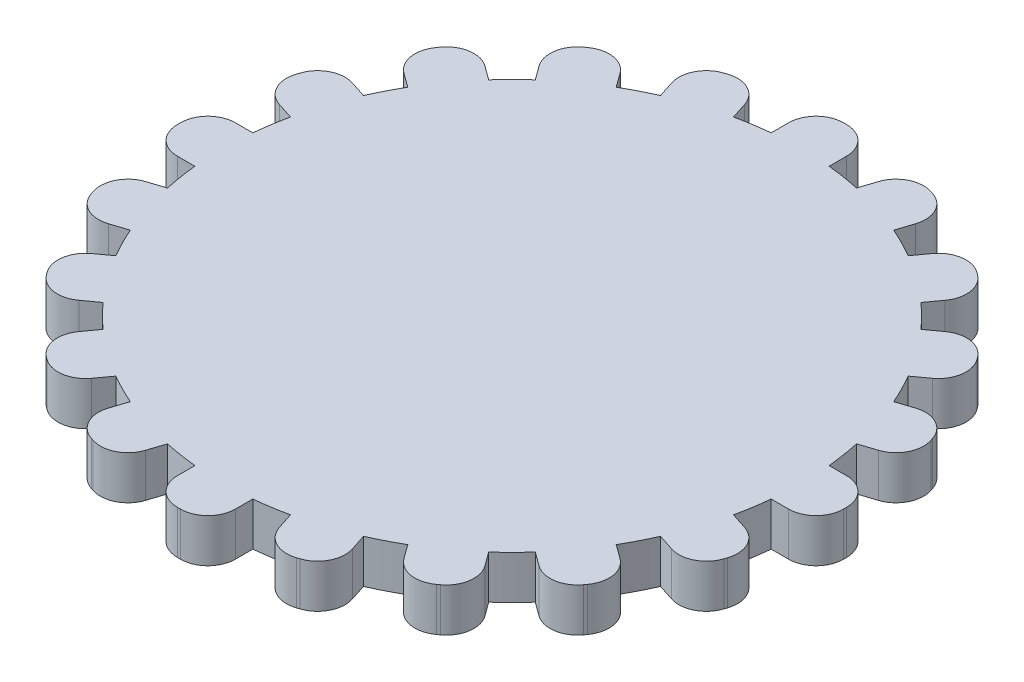
SolidWorks part; units mm, degrees
ref_plane "Front Plane" through (0, 0, 0) normal (0, 0, 1) x (1, 0, 0)
ref_plane "Top Plane" through (0, 0, 0) normal (0, 1, 0) x (1, 0, 0)
ref_plane "Right Plane" through (0, 0, 0) normal (1, 0, 0) x (0, 0, -1)
sketch "Sketch1" plane through (0, 0, 0) normal (0, 1, 0) x (1, 0, 0)
  line L0 (0, -10) -> (0, -1.5)
  line L50 (0, 1.5) -> (0, 10)
  line L51 (-2.5, -1.5) -> (2.5, -1.5)
  line L52 (-13, 0) -> (13, 0)
  line L53 (-13, -0.1) -> (-13, 0.1)
  line L54 (-11.1, 2) -> (-9.798, 2)
  line L55 (-11.1, -2) -> (-9.798, -2)
  line L56 (-2.5, -1.5) -> (-2.5, 1.5)
  line L57 (-7.8045, 8.1425) -> (-6.7511, 7.3771)
  line L58 (-10.576, 7.5603) -> (-10.4584, 7.7221)
  line L59 (-10.1557, 4.9064) -> (-9.1023, 4.1411)
  line L60 (-1.528, 11.1748) -> (-1.1256, 9.9364)
  line L61 (-4.1123, 12.3328) -> (-3.9221, 12.3946)
  line L62 (-5.3322, 9.9387) -> (-4.9298, 8.7004)
  line L63 (5.3322, 9.9387) -> (4.9298, 8.7004)
  line L64 (3.9221, 12.3946) -> (4.1123, 12.3328)
  line L65 (1.528, 11.1748) -> (1.1256, 9.9364)
  line L66 (10.1557, 4.9064) -> (9.1023, 4.1411)
  line L67 (10.4584, 7.7221) -> (10.576, 7.5603)
  line L68 (7.8045, 8.1425) -> (6.7511, 7.3771)
  line L69 (11.1, -2) -> (9.798, -2)
  line L70 (13, 0.1) -> (13, -0.1)
  line L71 (11.1, 2) -> (9.798, 2)
  line L72 (7.8045, -8.1425) -> (6.7511, -7.3771)
  line L73 (10.576, -7.5603) -> (10.4584, -7.7221)
  line L74 (10.1557, -4.9064) -> (9.1023, -4.1411)
  line L75 (1.528, -11.1748) -> (1.1256, -9.9364)
  line L76 (4.1123, -12.3328) -> (3.9221, -12.3946)
  line L77 (5.3322, -9.9387) -> (4.9298, -8.7004)
  line L78 (-5.3322, -9.9387) -> (-4.9298, -8.7004)
  line L79 (-3.9221, -12.3946) -> (-4.1123, -12.3328)
  line L80 (-1.528, -11.1748) -> (-1.1256, -9.9364)
  line L81 (-10.1557, -4.9064) -> (-9.1023, -4.1411)
  line L82 (-10.4584, -7.7221) -> (-10.576, -7.5603)
  line L83 (-7.8045, -8.1425) -> (-6.7511, -7.3771)
  line L84 (-2.5, 1.5) -> (2.5, 1.5)
  line L85 (2.5, -1.5) -> (2.5, 1.5)
  line L86 (-2.5, -1.5) -> (2.5, 1.5) construction
  line L87 (-2.5, 1.5) -> (2.5, -1.5) construction
  arc A13 (-9.1023, 4.1411) -> (-9.798, 2) centre (0, 0) ccw
  arc A14 (-13, 0.1) -> (-11.1, 2) centre (-11.1, 0.1) cw
  arc A15 (-13, -0.1) -> (-11.1, -2) centre (-11.1, -0.1) ccw
  arc A16 (-10.4584, 7.7221) -> (-7.8045, 8.1425) centre (-8.9213, 6.6053) cw
  arc A17 (-10.576, 7.5603) -> (-10.1557, 4.9064) centre (-9.0389, 6.4435) ccw
  arc A18 (-3.9221, 12.3946) -> (-1.528, 11.1748) centre (-3.335, 10.5876) cw
  arc A19 (-4.1123, 12.3328) -> (-5.3322, 9.9387) centre (-3.5252, 10.5258) ccw
  arc A20 (4.1123, 12.3328) -> (5.3322, 9.9387) centre (3.5252, 10.5258) cw
  arc A21 (3.9221, 12.3946) -> (1.528, 11.1748) centre (3.335, 10.5876) ccw
  arc A22 (10.576, 7.5603) -> (10.1557, 4.9064) centre (9.0389, 6.4435) cw
  arc A23 (10.4584, 7.7221) -> (7.8045, 8.1425) centre (8.9213, 6.6053) ccw
  arc A24 (13, -0.1) -> (11.1, -2) centre (11.1, -0.1) cw
  arc A25 (13, 0.1) -> (11.1, 2) centre (11.1, 0.1) ccw
  arc A26 (10.4584, -7.7221) -> (7.8045, -8.1425) centre (8.9213, -6.6053) cw
  arc A27 (10.576, -7.5603) -> (10.1557, -4.9064) centre (9.0389, -6.4435) ccw
  arc A28 (3.9221, -12.3946) -> (1.528, -11.1748) centre (3.335, -10.5876) cw
  arc A29 (4.1123, -12.3328) -> (5.3322, -9.9387) centre (3.5252, -10.5258) ccw
  arc A30 (-4.1123, -12.3328) -> (-5.3322, -9.9387) centre (-3.5252, -10.5258) cw
  arc A31 (-3.9221, -12.3946) -> (-1.528, -11.1748) centre (-3.335, -10.5876) ccw
  arc A32 (-10.576, -7.5603) -> (-10.1557, -4.9064) centre (-9.0389, -6.4435) cw
  arc A33 (-10.4584, -7.7221) -> (-7.8045, -8.1425) centre (-8.9213, -6.6053) ccw
  arc A34 (-4.9298, 8.7004) -> (-6.7511, 7.3771) centre (0, 0) ccw
  arc A35 (1.1256, 9.9364) -> (-1.1256, 9.9364) centre (0, 0) ccw
  arc A36 (6.7511, 7.3771) -> (4.9298, 8.7004) centre (0, 0) ccw
  arc A37 (9.798, 2) -> (9.1023, 4.1411) centre (0, 0) ccw
  arc A38 (9.1023, -4.1411) -> (9.798, -2) centre (0, 0) ccw
  arc A39 (4.9298, -8.7004) -> (6.7511, -7.3771) centre (0, 0) ccw
  arc A40 (-1.1256, -9.9364) -> (1.1256, -9.9364) centre (0, 0) ccw
  arc A41 (-6.7511, -7.3771) -> (-4.9298, -8.7004) centre (0, 0) ccw
  arc A42 (-9.798, -2) -> (-9.1023, -4.1411) centre (0, 0) ccw
  point P6 (0, 0)
  point P8 (0, 0)
  point P9 (0, 0)
  point P17 (0, 0)
  point P18 (0, 0)
  point P22 (-13, 2)
  point P63 (0, 0)
  point P119 (0, 0)
  dimension "D1" = 20
  dimension "D2" = 26
  dimension "D4" = 1.9
  dimension "D3" = 2
  dimension "D5" = 10
  dimension "D6" = 3
  dimension "D7" = 5
sketch "Sketch2" plane through (0, 0, 0) normal (0, 1, 0) x (1, 0, 0)
  line L0 (-2, 0) -> (2, 0)
  line L1 (-23, -0.1) -> (-23, 0.1)
  line L2 (-21.1, 2) -> (-19.8997, 2)
  line L3 (-21.1, -2) -> (-19.8997, -2)
  line L4 (-20.6853, 4.6181) -> (-19.5438, 4.2472)
  line L5 (-19.4493, 8.4224) -> (-18.3078, 8.0515)
  line L6 (-21.9052, 7.0123) -> (-21.8434, 7.2025)
  line L7 (-18.2458, 10.7842) -> (-17.2748, 10.0787)
  line L8 (-15.8947, 14.0203) -> (-14.9237, 13.3148)
  line L9 (-18.6662, 13.4382) -> (-18.5486, 13.6)
  line L10 (-14.0203, 15.8947) -> (-13.3148, 14.9237)
  line L11 (-10.7842, 18.2458) -> (-10.0787, 17.2748)
  line L12 (-13.6, 18.5486) -> (-13.4382, 18.6662)
  line L13 (-8.4224, 19.4493) -> (-8.0515, 18.3078)
  line L14 (-4.6181, 20.6853) -> (-4.2472, 19.5438)
  line L15 (-7.2025, 21.8434) -> (-7.0123, 21.9052)
  line L16 (-2, 21.1) -> (-2, 19.8997)
  line L17 (2, 21.1) -> (2, 19.8997)
  line L18 (-0.1, 23) -> (0.1, 23)
  line L19 (4.6181, 20.6853) -> (4.2472, 19.5438)
  line L20 (8.4224, 19.4493) -> (8.0515, 18.3078)
  line L21 (7.0123, 21.9052) -> (7.2025, 21.8434)
  line L22 (10.7842, 18.2458) -> (10.0787, 17.2748)
  line L23 (14.0203, 15.8947) -> (13.3148, 14.9237)
  line L24 (13.4382, 18.6662) -> (13.6, 18.5486)
  line L25 (15.8947, 14.0203) -> (14.9237, 13.3148)
  line L26 (18.2458, 10.7842) -> (17.2748, 10.0787)
  line L27 (18.5486, 13.6) -> (18.6662, 13.4382)
  line L28 (19.4493, 8.4224) -> (18.3078, 8.0515)
  line L29 (20.6853, 4.6181) -> (19.5438, 4.2472)
  line L30 (21.8434, 7.2025) -> (21.9052, 7.0123)
  line L31 (21.1, 2) -> (19.8997, 2)
  line L32 (21.1, -2) -> (19.8997, -2)
  line L33 (23, 0.1) -> (23, -0.1)
  line L34 (20.6853, -4.6181) -> (19.5438, -4.2472)
  line L35 (19.4493, -8.4224) -> (18.3078, -8.0515)
  line L36 (21.9052, -7.0123) -> (21.8434, -7.2025)
  line L37 (18.2458, -10.7842) -> (17.2748, -10.0787)
  line L38 (15.8947, -14.0203) -> (14.9237, -13.3148)
  line L39 (18.6662, -13.4382) -> (18.5486, -13.6)
  line L40 (14.0203, -15.8947) -> (13.3148, -14.9237)
  line L41 (10.7842, -18.2458) -> (10.0787, -17.2748)
  line L42 (13.6, -18.5486) -> (13.4382, -18.6662)
  line L43 (8.4224, -19.4493) -> (8.0515, -18.3078)
  line L44 (4.6181, -20.6853) -> (4.2472, -19.5438)
  line L45 (7.2025, -21.8434) -> (7.0123, -21.9052)
  line L46 (2, -21.1) -> (2, -19.8997)
  line L47 (-2, -21.1) -> (-2, -19.8997)
  line L48 (0.1, -23) -> (-0.1, -23)
  line L49 (-4.6181, -20.6853) -> (-4.2472, -19.5438)
  line L50 (-8.4224, -19.4493) -> (-8.0515, -18.3078)
  line L51 (-7.0123, -21.9052) -> (-7.2025, -21.8434)
  line L52 (-10.7842, -18.2458) -> (-10.0787, -17.2748)
  line L53 (-14.0203, -15.8947) -> (-13.3148, -14.9237)
  line L54 (-13.4382, -18.6662) -> (-13.6, -18.5486)
  line L55 (-15.8947, -14.0203) -> (-14.9237, -13.3148)
  line L56 (-18.2458, -10.7842) -> (-17.2748, -10.0787)
  line L57 (-18.5486, -13.6) -> (-18.6662, -13.4382)
  line L58 (-19.4493, -8.4224) -> (-18.3078, -8.0515)
  line L59 (-20.6853, -4.6181) -> (-19.5438, -4.2472)
  line L60 (-21.8434, -7.2025) -> (-21.9052, -7.0123)
  arc A0 (-18.3078, -8.0515) -> (-17.2748, -10.0787) centre (0, 0) ccw
  arc A1 (-21.1, 2) -> (-23, 0.1) centre (-21.1, 0.1) ccw
  arc A2 (-21.1, -2) -> (-23, -0.1) centre (-21.1, -0.1) cw
  arc A3 (-20.6853, 4.6181) -> (-21.9052, 7.0123) centre (-20.0982, 6.4252) cw
  arc A4 (-19.4493, 8.4224) -> (-21.8434, 7.2025) centre (-20.0364, 6.6154) ccw
  arc A5 (-18.2458, 10.7842) -> (-18.6662, 13.4382) centre (-17.129, 12.3214) cw
  arc A6 (-15.8947, 14.0203) -> (-18.5486, 13.6) centre (-17.0115, 12.4832) ccw
  arc A7 (-14.0203, 15.8947) -> (-13.6, 18.5486) centre (-12.4832, 17.0115) cw
  arc A8 (-10.7842, 18.2458) -> (-13.4382, 18.6662) centre (-12.3214, 17.129) ccw
  arc A9 (-8.4224, 19.4493) -> (-7.2025, 21.8434) centre (-6.6154, 20.0364) cw
  arc A10 (-4.6181, 20.6853) -> (-7.0123, 21.9052) centre (-6.4252, 20.0982) ccw
  arc A11 (-2, 21.1) -> (-0.1, 23) centre (-0.1, 21.1) cw
  arc A12 (2, 21.1) -> (0.1, 23) centre (0.1, 21.1) ccw
  arc A13 (4.6181, 20.6853) -> (7.0123, 21.9052) centre (6.4252, 20.0982) cw
  arc A14 (8.4224, 19.4493) -> (7.2025, 21.8434) centre (6.6154, 20.0364) ccw
  arc A15 (10.7842, 18.2458) -> (13.4382, 18.6662) centre (12.3214, 17.129) cw
  arc A16 (14.0203, 15.8947) -> (13.6, 18.5486) centre (12.4832, 17.0115) ccw
  arc A17 (15.8947, 14.0203) -> (18.5486, 13.6) centre (17.0115, 12.4832) cw
  arc A18 (18.2458, 10.7842) -> (18.6662, 13.4382) centre (17.129, 12.3214) ccw
  arc A19 (19.4493, 8.4224) -> (21.8434, 7.2025) centre (20.0364, 6.6154) cw
  arc A20 (20.6853, 4.6181) -> (21.9052, 7.0123) centre (20.0982, 6.4252) ccw
  arc A21 (21.1, 2) -> (23, 0.1) centre (21.1, 0.1) cw
  arc A22 (21.1, -2) -> (23, -0.1) centre (21.1, -0.1) ccw
  arc A23 (20.6853, -4.6181) -> (21.9052, -7.0123) centre (20.0982, -6.4252) cw
  arc A24 (19.4493, -8.4224) -> (21.8434, -7.2025) centre (20.0364, -6.6154) ccw
  arc A25 (18.2458, -10.7842) -> (18.6662, -13.4382) centre (17.129, -12.3214) cw
  arc A26 (15.8947, -14.0203) -> (18.5486, -13.6) centre (17.0115, -12.4832) ccw
  arc A27 (14.0203, -15.8947) -> (13.6, -18.5486) centre (12.4832, -17.0115) cw
  arc A28 (10.7842, -18.2458) -> (13.4382, -18.6662) centre (12.3214, -17.129) ccw
  arc A29 (8.4224, -19.4493) -> (7.2025, -21.8434) centre (6.6154, -20.0364) cw
  arc A30 (4.6181, -20.6853) -> (7.0123, -21.9052) centre (6.4252, -20.0982) ccw
  arc A31 (2, -21.1) -> (0.1, -23) centre (0.1, -21.1) cw
  arc A32 (-2, -21.1) -> (-0.1, -23) centre (-0.1, -21.1) ccw
  arc A33 (-4.6181, -20.6853) -> (-7.0123, -21.9052) centre (-6.4252, -20.0982) cw
  arc A34 (-8.4224, -19.4493) -> (-7.2025, -21.8434) centre (-6.6154, -20.0364) ccw
  arc A35 (-10.7842, -18.2458) -> (-13.4382, -18.6662) centre (-12.3214, -17.129) cw
  arc A36 (-14.0203, -15.8947) -> (-13.6, -18.5486) centre (-12.4832, -17.0115) ccw
  arc A37 (-15.8947, -14.0203) -> (-18.5486, -13.6) centre (-17.0115, -12.4832) cw
  arc A38 (-18.2458, -10.7842) -> (-18.6662, -13.4382) centre (-17.129, -12.3214) ccw
  arc A39 (-19.4493, -8.4224) -> (-21.8434, -7.2025) centre (-20.0364, -6.6154) cw
  arc A40 (-20.6853, -4.6181) -> (-21.9052, -7.0123) centre (-20.0982, -6.4252) ccw
  arc A41 (-19.8997, -2) -> (-19.5438, -4.2472) centre (0, 0) ccw
  arc A42 (-19.5438, 4.2472) -> (-19.8997, 2) centre (0, 0) ccw
  arc A43 (-17.2748, 10.0787) -> (-18.3078, 8.0515) centre (0, 0) ccw
  arc A44 (-13.3148, 14.9237) -> (-14.9237, 13.3148) centre (0, 0) ccw
  arc A45 (-8.0515, 18.3078) -> (-10.0787, 17.2748) centre (0, 0) ccw
  arc A46 (-2, 19.8997) -> (-4.2472, 19.5438) centre (0, 0) ccw
  arc A47 (4.2472, 19.5438) -> (2, 19.8997) centre (0, 0) ccw
  arc A48 (10.0787, 17.2748) -> (8.0515, 18.3078) centre (0, 0) ccw
  arc A49 (14.9237, 13.3148) -> (13.3148, 14.9237) centre (0, 0) ccw
  arc A50 (18.3078, 8.0515) -> (17.2748, 10.0787) centre (0, 0) ccw
  arc A51 (19.8997, 2) -> (19.5438, 4.2472) centre (0, 0) ccw
  arc A52 (19.5438, -4.2472) -> (19.8997, -2) centre (0, 0) ccw
  arc A53 (17.2748, -10.0787) -> (18.3078, -8.0515) centre (0, 0) ccw
  arc A54 (13.3148, -14.9237) -> (14.9237, -13.3148) centre (0, 0) ccw
  arc A55 (8.0515, -18.3078) -> (10.0787, -17.2748) centre (0, 0) ccw
  arc A56 (2, -19.8997) -> (4.2472, -19.5438) centre (0, 0) ccw
  arc A57 (-10.0787, -17.2748) -> (-8.0515, -18.3078) centre (0, 0) ccw
  arc A58 (-4.2472, -19.5438) -> (-2, -19.8997) centre (0, 0) ccw
  arc A59 (-14.9237, -13.3148) -> (-13.3148, -14.9237) centre (0, 0) ccw
  point P6 (0, 0)
  point P10 (-23, 2)
  point P170 (0, 0)
  dimension "D1" = 40
  dimension "D4" = 1.9
  dimension "D5" = 20
extrude "Boss-Extrude3" add sketch "Sketch2" along normal blind 3
extrude "Boss-Extrude4" add sketch "Sketch1" along normal blind 3 separate body contours L50 A35 L60 A18 L61 A19 L62 A34 L57 A16 L58 A17 L59 A13 L54 A14 L53 L52 L56 L84 | L71 A37 L66 A22 L67 A23 L68 A36 L63 A20 L64 A21 L65 A35 L50 L84 L85 L52 L70 A25 | L0 A40 L75 A28 L76 A29 L77 A39 L72 A26 L73 A27 L74 A38 L69 A24 L70 L52 L85 L51 | L55 A42 L81 A32 L82 A33 L83 A41 L78 A30 L79 A31 L80 A40 L0 L51 L56 L52 L53 A15
